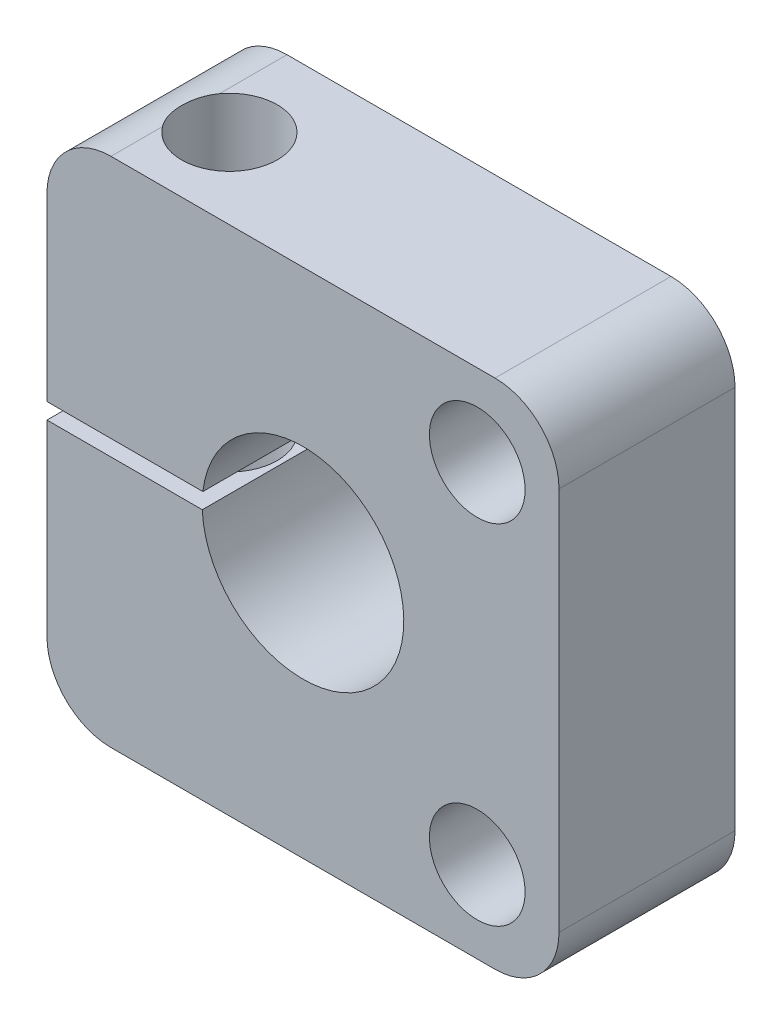
SolidWorks part; units mm, degrees
ref_plane "Front Plane" through (0, 0, 0) normal (0, 0, 1) x (1, 0, 0)
ref_plane "Top Plane" through (0, 0, 0) normal (0, 1, 0) x (1, 0, 0)
ref_plane "Right Plane" through (0, 0, 0) normal (1, 0, 0) x (0, 0, -1)
sketch "Sketch1" plane through (0, 0, 0) normal (0, 0, 1) x (1, 0, 0)
  line L1 (-10.16, 10.16) -> (10.16, 10.16)
  line L2 (-10.16, 10.16) -> (-10.16, -10.16)
  line L3 (-10.16, -10.16) -> (10.16, -10.16)
  line L4 (10.16, 10.16) -> (10.16, -10.16)
  line L5 (-10.16, 10.16) -> (10.16, -10.16) construction
  line L6 (-10.16, -10.16) -> (10.16, 10.16) construction
  point P0 (0, 0)
  dimension "D1" = 20.32
  dimension "D2" = 20.32
extrude "Boss-Extrude1" add sketch "Sketch1" along normal blind 6.985
sketch "Sketch4" plane through (0, 0, 6.985) normal (0, 0, 1) x (1, 0, 0)
  line L2 (0, 0) -> (-6.9148, 6.9148) construction
  dimension "D4" = 9.779
sketch "Sketch5" plane through (0, 0, 6.985) normal (0, 0, 1) x (1, 0, 0)
  line L1 (-3.7074, 0.4618) -> (-26.5674, 0.4618)
  line L2 (-3.7074, 0.4618) -> (-3.7074, -0.1732)
  line L3 (-3.7074, -0.1732) -> (-26.5674, -0.1732)
  line L4 (-26.5674, 0.4618) -> (-26.5674, -0.1732)
  dimension "D1" = 22.86
  dimension "D2" = 0.635
extrude "Cut-Extrude3" cut sketch "Sketch5" against normal through all both and the other way through all
hole_wizard "#6 Clearance Hole1" positions "Sketch6" profile "Sketch7" hole size "#6" standard "ANSI Inch" end condition up to next
sketch "Sketch6" plane through (0, 0, 6.985) normal (0, 0, 1) x (1, 0, 0)
  line L2 (10.16, -10.16) -> (10.16, 10.16) construction
  line L4 (-10.16, -10.16) -> (10.16, -10.16) construction
  point P23 (6.9148, 6.9148)
  point P24 (6.9148, -6.9148)
  dimension "D1" = 3.2452
  dimension "D3" = 9.779
  dimension "D4" = 9.779
  dimension "D5" = 3.2452
sketch "Sketch7" plane through (6.9148, 6.9148, 6.985) normal (1, 0, 0) x (0, -1, 0)
  line L0 (0, 0) -> (0, 6.985)
  line L1 (0, 6.985) -> (1.8986, 6.985)
  line L2 (1.8986, 6.985) -> (1.8986, 0)
  line L5 (1.8986, 0) -> (0, 0)
  line L11 (0, -6.35) -> (0, 107.95) construction
  dimension "Thru Hole Dia." = 3.7973
  dimension "Thru Hole Depth" = 6.985
fillet "Fillet1" radius 2.54 4 edges at (10.16, -10.16, 3.4925) (-10.16, -10.16, 3.4925) (10.16, 10.16, 3.4925) (-10.16, 10.16, 3.4925)
hole_wizard "Ø8.0mm Dowel Hole1" positions "Sketch8" profile "Sketch9" hole size "Ø8.0" standard "ANSI Metric" end condition up to next
sketch "Sketch8" plane through (0, 0, 6.985) normal (0, 0, 1) x (1, 0, 0)
  point P0 (0, 0)
sketch "Sketch9" plane through (0, 0, 6.985) normal (1, 0, 0) x (0, -1, 0)
  line L0 (0, 0) -> (0, 6.985)
  line L1 (0, 6.985) -> (4, 6.985)
  line L2 (4, 6.985) -> (4, 0)
  line L5 (4, 0) -> (0, 0)
  line L11 (0, -6.35) -> (0, 107.95) construction
  dimension "Thru Hole Dia." = 8
  dimension "Thru Hole Depth" = 6.985
hole_wizard "#6 Clearance Hole2" positions "Sketch10" profile "Sketch11" hole size "#6" standard "ANSI Inch" end condition through all
sketch "Sketch10" plane through (0, 10.16, 0) normal (0, 1, 0) x (1, 0, 0)
  line L0 (-7.62, 0) -> (-7.62, -6.985) construction
  line L1 (7.62, -6.985) -> (-7.62, -6.985) construction
  point P0 (-6.096, -3.81)
  dimension "D1" = 1.524
  dimension "D2" = 3.175
sketch "Sketch11" plane through (-6.096, 10.16, 3.81) normal (1, 0, 0) x (0, 0, 1)
  line L0 (0, 0) -> (0, 20.32)
  line L1 (0, 20.32) -> (1.8986, 20.32)
  line L2 (1.8986, 20.32) -> (1.8986, 0)
  line L5 (1.8986, 0) -> (0, 0)
  line L11 (0, -6.35) -> (0, 107.95) construction
  dimension "Thru Hole Dia." = 3.7973
  dimension "Thru Hole Depth" = 20.32
